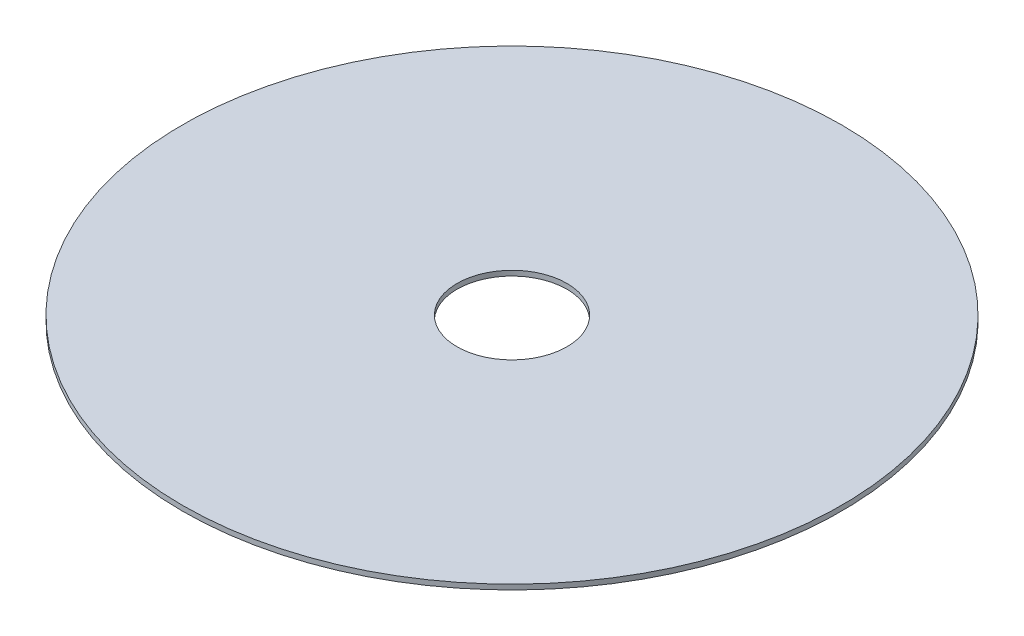
SolidWorks part; units mm, degrees
material "AISI 1020"
ref_plane "Front Plane" through (0, 0, 0) normal (0, 0, 1) x (1, 0, 0)
ref_plane "Top Plane" through (0, 0, 0) normal (0, 1, 0) x (1, 0, 0)
ref_plane "Right Plane" through (0, 0, 0) normal (1, 0, 0) x (0, 0, -1)
sketch "Sketch1" plane through (0, 0, 0) normal (0, 0, 1) x (1, 0, 0)
  line L0 (0, 0) -> (0, 30.5205) construction
  line L1 (0, 0) -> (250, 0)
  line L2 (250, 11.5) -> (250, -11.5)
  line L3 (250, 11.5) -> (1500, 11.5)
  line L4 (1500, 11.5) -> (1500, -11.5)
  line L5 (1500, -11.5) -> (250, -11.5)
  point P7 (250, 0)
revolve "Revolve1" add sketch "Sketch1" angle 360 about L0
sketch "Sketch2" plane through (0, 11.5, 0) normal (0, 1, 0) x (1, 0, 0)
  line L0 (0, -1460) -> (0, 1460)
  line L1 (-1460, 0) -> (1460, 0) construction
  line L2 (0, 0) -> (1348.8641, 558.7178) construction
  line L3 (0, 0) -> (558.7178, 1348.8641) construction
  line L4 (0, 0) -> (-1348.8641, 558.7178) construction
  line L5 (0, 0) -> (-558.7178, 1348.8641) construction
  line L6 (0, 0) -> (1348.8641, -558.7178) construction
  line L7 (0, 0) -> (558.7178, -1348.8641) construction
  line L8 (0, 0) -> (-1348.8641, -558.7178) construction
  line L9 (0, 0) -> (-558.7178, -1348.8641) construction
  arc A0 (1348.8641, 558.7178) -> (558.7178, 1348.8641) centre (0, 0) ccw construction
  circle A6 centre (0, 1460) radius 30 construction
  circle A8 centre (-1460, 0) radius 30 construction
  circle A9 centre (1460, 0) radius 30 construction
  circle A10 centre (0, -1460) radius 30 construction
  arc A11 (886.9244, 367.3761) -> (367.3761, 886.9244) centre (0, 0) ccw construction
  arc A12 (-1348.8641, 558.7178) -> (-558.7178, 1348.8641) centre (0, 0) cw construction
  arc A13 (-886.9244, 367.3761) -> (-367.3761, 886.9244) centre (0, 0) cw construction
  arc A14 (1348.8641, -558.7178) -> (558.7178, -1348.8641) centre (0, 0) cw construction
  arc A15 (886.9244, -367.3761) -> (367.3761, -886.9244) centre (0, 0) cw construction
  arc A16 (-1348.8641, -558.7178) -> (-558.7178, -1348.8641) centre (0, 0) ccw construction
  arc A17 (-886.9244, -367.3761) -> (-367.3761, -886.9244) centre (0, 0) ccw construction
  point P7 (0, 0)
  point P8 (0, 0)
